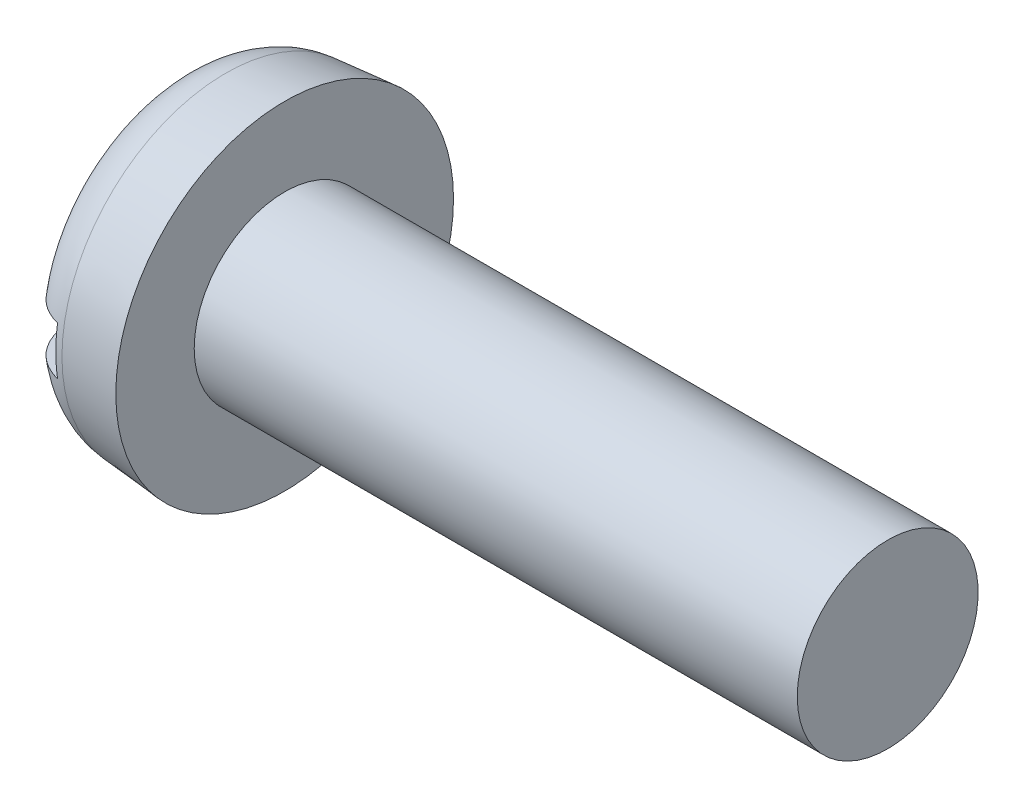
SolidWorks part; units mm, degrees
ref_plane "Plane1" through (0, 0, 0) normal (0, 0, 1) x (1, 0, 0)
ref_plane "Plane2" through (0, 0, 0) normal (0, 1, 0) x (1, 0, 0)
ref_plane "Plane3" through (0, 0, 0) normal (1, 0, 0) x (0, 0, -1)
sketch "BodySke" plane through (0, 0, 0) normal (0, 0, 1) x (1, 0, 0)
  line L0 (1.8, 1.5) -> (1.8, 2.8)
  line L1 (0, 0) -> (0, 2.6425)
  line L2 (-25.4, 0) -> (127, 0) construction
  line L3 (11.8, 0) -> (0, 0)
  line L4 (1.8, 1.5) -> (11.8, 1.5)
  line L5 (11.8, 1.5) -> (11.8, 0)
  line L6 (0, 2.6425) -> (1.8, 2.8)
  line L9 (2.3, 3.0875) -> (2.3, -6.4375) construction
  line L10 (1.8, 6.35) -> (1.8, -3.175) construction
  dimension "Head_ht" = 1.8
  dimension "Diameter" = 3
  dimension "Length" = 10
  dimension "Head_dia" = 5.6
  dimension "Advance" = 0.5
  dimension "Thread_nom" = 10
  dimension "Head_side_angle" = 5
revolve "Base-Revolve" add sketch "BodySke"
cosmetic thread "ThreadCosmetic"
fillet "Fillet1" [suppressed] radius 0.1
fillet "Fillet2" radius 0.9 1 edges at (0, 0, 2.6425)
sketch "Sketch2" plane through (0, 0, 0) normal (1, 0, 0) x (0, 0, -1)
  line L0 (2.8, -0.4) -> (-2.8, -0.4)
  line L1 (2.8, -0.4) -> (2.8, 0.4)
  line L2 (-2.8, 0.4) -> (2.8, 0.4)
  line L3 (-2.8, 0.4) -> (-2.8, -0.4)
  dimension "D1" = 5.6
  dimension "D2" = 2.8
  dimension "Slot_width" = 0.8
  dimension "D3" = 0.4
extrude "Slot" cut sketch "Sketch2" along normal blind 0.7
sketch "ThdSchSke" plane through (0, 0, 0) normal (0, 0, 1) x (1, 0, 0)
  line L0 (2.8, -1.2195) -> (2.6036, -1.5)
  line L1 (2.8, -1.2195) -> (2.9964, -1.5)
  line L2 (2.9964, -1.5) -> (2.9964, -1.875)
  line L3 (-3.175, 0) -> (5.1513, 0) construction
  line L5 (2.9964, -1.875) -> (2.6036, -1.875)
  line L6 (2.6036, -1.875) -> (2.6036, -1.5)
  dimension "Thread_minor" = 2.439
  dimension "Diameter" = 3
  dimension "Start" = 2.8
  dimension "SideAngle" = 55
  dimension "VeeAngle" = 70
  dimension "Overcut" = 3.75
revolve "ThreadSchematic" [suppressed] cut sketch "ThdSchSke" angle 360 about L3
pattern_linear "ThdSchPat" [suppressed]
equation "\"D1@Sketch2\" = \"Head_dia@BodySke\""
equation "\"D2@Sketch2\" = \"D1@Sketch2\" / 2"
equation "\"D3@Sketch2\" = \"Slot_width@Sketch2\" / 2"
equation "\"Thread_length@ThreadCosmetic\" = ((sgn( (\"Length@BodySke\" - \"Advance@BodySke\" * 2.0 ) - \"Thread_nom@BodySke\" )-1)*( (\"Length@BodySke\" - \"Advance@BodySke\"  * 2.0) - \"Thread_nom@BodySke\" ))/-2+ \"Thread_nom@BodySke\""
equation "\"Thread_minor@ThdSchSke\" = \"Thread_minor@ThreadCosmetic\""
equation "\"Diameter@ThdSchSke\" = \"Diameter@BodySke\""
equation "\"Overcut@ThdSchSke\" = \"Diameter@BodySke\" * 1.25"
equation "\"Start@ThdSchSke\" = \"Head_ht@BodySke\" + \"Length@BodySke\" - \"Thread_length@ThreadCosmetic\"  '---Non-countersunk---"
equation "\"Num_threads@ThdSchPat\" = int( \"Thread_length@ThreadCosmetic\" / \"Advance@BodySke\" + 0.999 )  + 1"
equation "\"Advance@ThdSchPat\" = \"Thread_length@ThreadCosmetic\" /  (\"Num_threads@ThdSchPat\" - 1) 'relax it"
